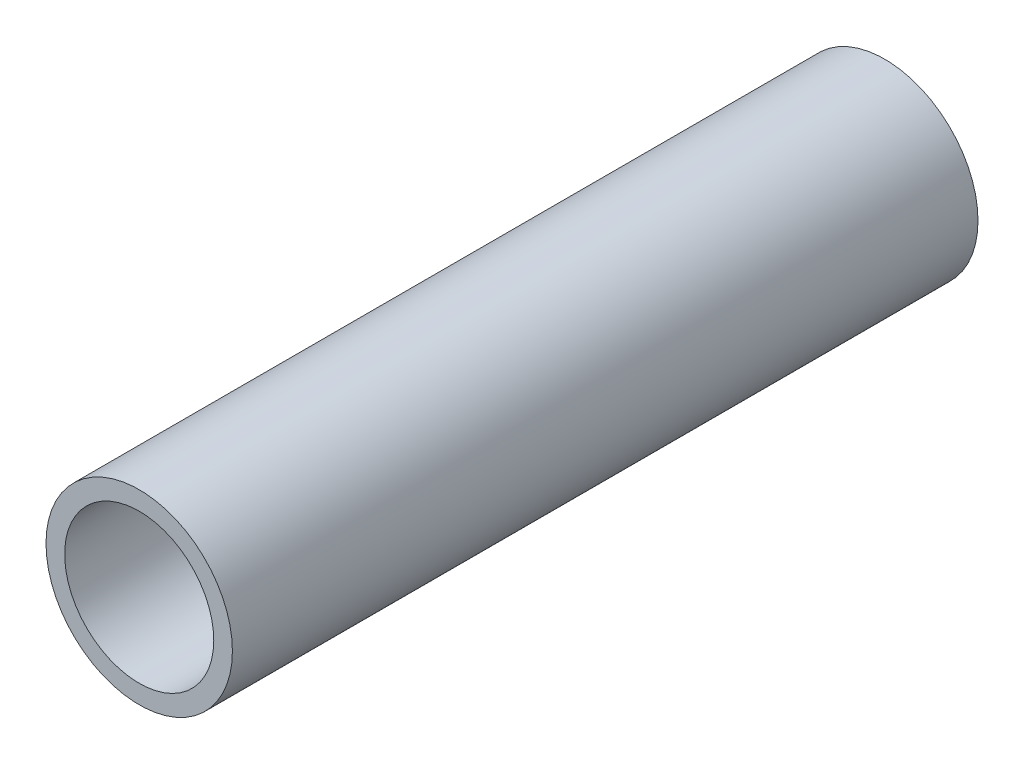
SolidWorks part; units mm, degrees
ref_plane "正面" through (0, 0, 0) normal (0, 0, 1) x (1, 0, 0)
ref_plane "平面" through (0, 0, 0) normal (0, 1, 0) x (1, 0, 0)
ref_plane "右側面" through (0, 0, 0) normal (1, 0, 0) x (0, 0, -1)
sketch "ｽｹｯﾁ1" plane through (0, 0, 0) normal (0, 0, 1) x (1, 0, 0)
  circle A0 centre (0, 0) radius 2.5
  circle A1 centre (0, 0) radius 2
  dimension "D1" = 5
  dimension "D2" = 4
extrude "ﾎﾞｽ - 押し出し1" add sketch "ｽｹｯﾁ1" along normal blind 20 contours A1 | A0
